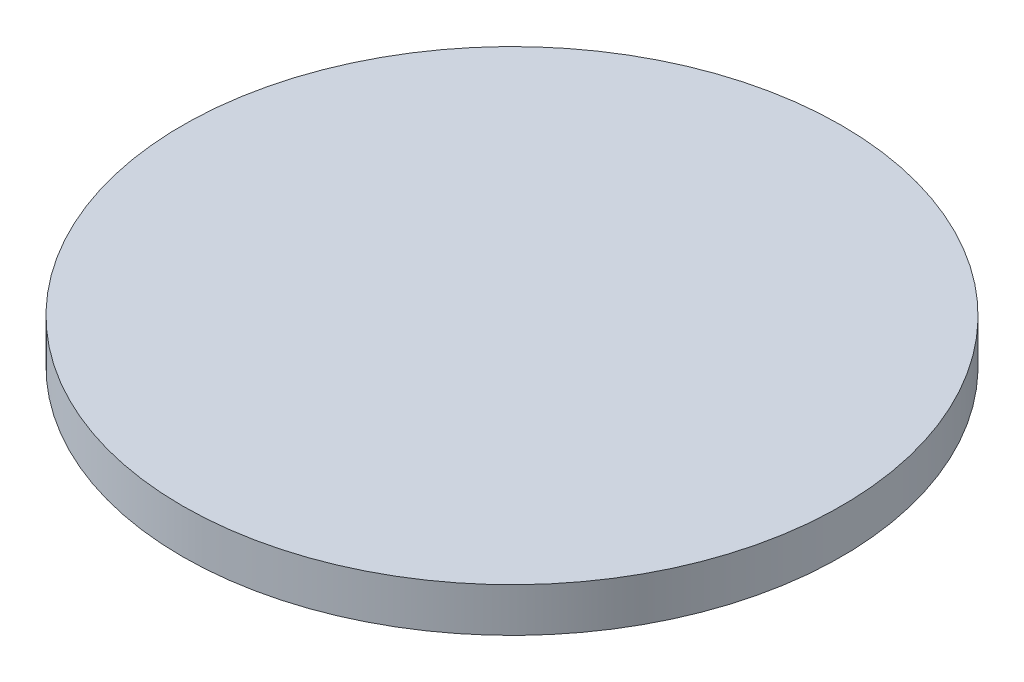
SolidWorks part; units mm, degrees
ref_plane "Plan de face" through (0, 0, 0) normal (0, 0, 1) x (1, 0, 0)
ref_plane "Plan de dessus" through (0, 0, 0) normal (0, 1, 0) x (1, 0, 0)
ref_plane "Plan de droite" through (0, 0, 0) normal (1, 0, 0) x (0, 0, -1)
sketch "Esquisse1" plane through (0, 0, 0) normal (0, 1, 0) x (1, 0, 0)
  circle A0 centre (0, 0) radius 22.5
  dimension "D1" = 45
extrude "Boss.-Extru.1" add sketch "Esquisse1" along normal mid plane 3
